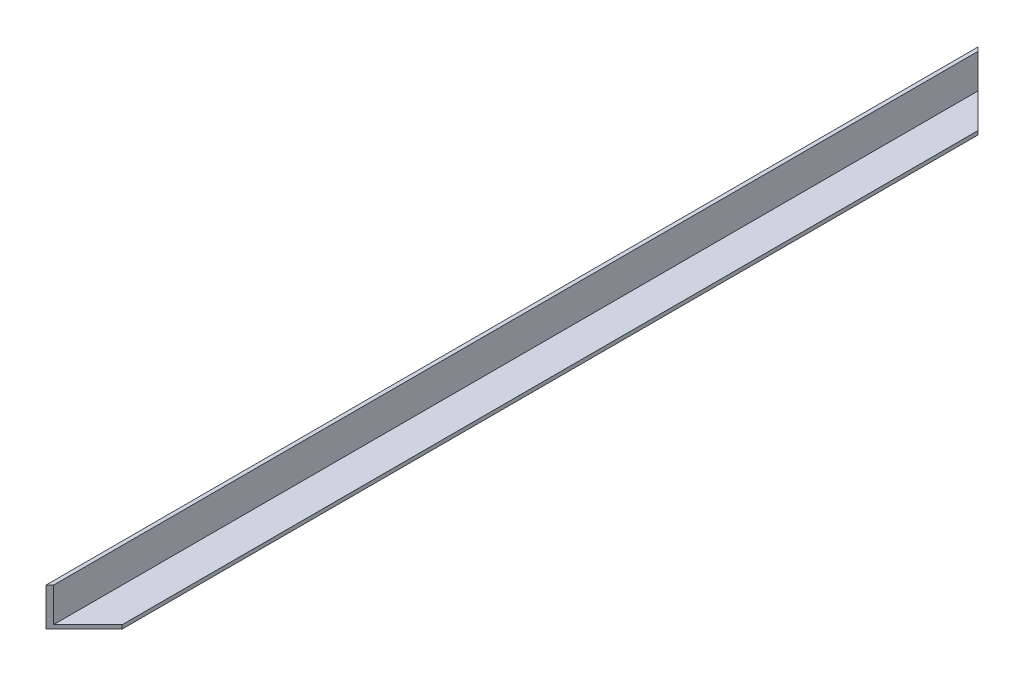
SolidWorks part; units mm, degrees
ref_plane "Front Plane" through (0, 0, 0) normal (0, 0, 1) x (1, 0, 0)
ref_plane "Top Plane" through (0, 0, 0) normal (0, 1, 0) x (1, 0, 0)
ref_plane "Right Plane" through (0, 0, 0) normal (1, 0, 0) x (0, 0, -1)
sketch "Sketch1" plane through (0, 0, 0) normal (0, 0, 1) x (1, 0, 0)
  line L0 (0, 20) -> (0, 0)
  line L1 (0, 0) -> (20, 0)
  line L2 (20, 0) -> (20, 2)
  line L3 (20, 2) -> (2, 2)
  line L4 (2, 2) -> (2, 20)
  line L5 (2, 20) -> (0, 20)
  dimension "D1" = 20
  dimension "D2" = 20
  dimension "D3" = 2
  dimension "D4" = 2
extrude "Boss-Extrude1" add sketch "Sketch1" along normal blind 489
sketch "Sketch2" plane through (0, 20, 0) normal (0, 1, 0) x (1, 0, 0)
  line L0 (0, 0) -> (20, -20)
  line L1 (20, -489) -> (20, 0) construction
  line L2 (20, -20) -> (20, 0)
  line L3 (20, 0) -> (0, 0)
  line L4 (0, -489) -> (20, -469)
  line L5 (20, -469) -> (20, -489)
  line L6 (20, -489) -> (0, -489)
  line M1 (2, 0) -> (0, 0)
  line M3 (0, -489) -> (2, -489)
  line M4 (2, -489) -> (2, 0)
  dimension "D1" = 45
  dimension "D2" = 45
extrude "Cut-Extrude2" cut sketch "Sketch2" against normal blind 485 contours L0 M1 M4 | L2 L3 L0 M4 | L4 M3 M4 | L6 L5 L4 M4
